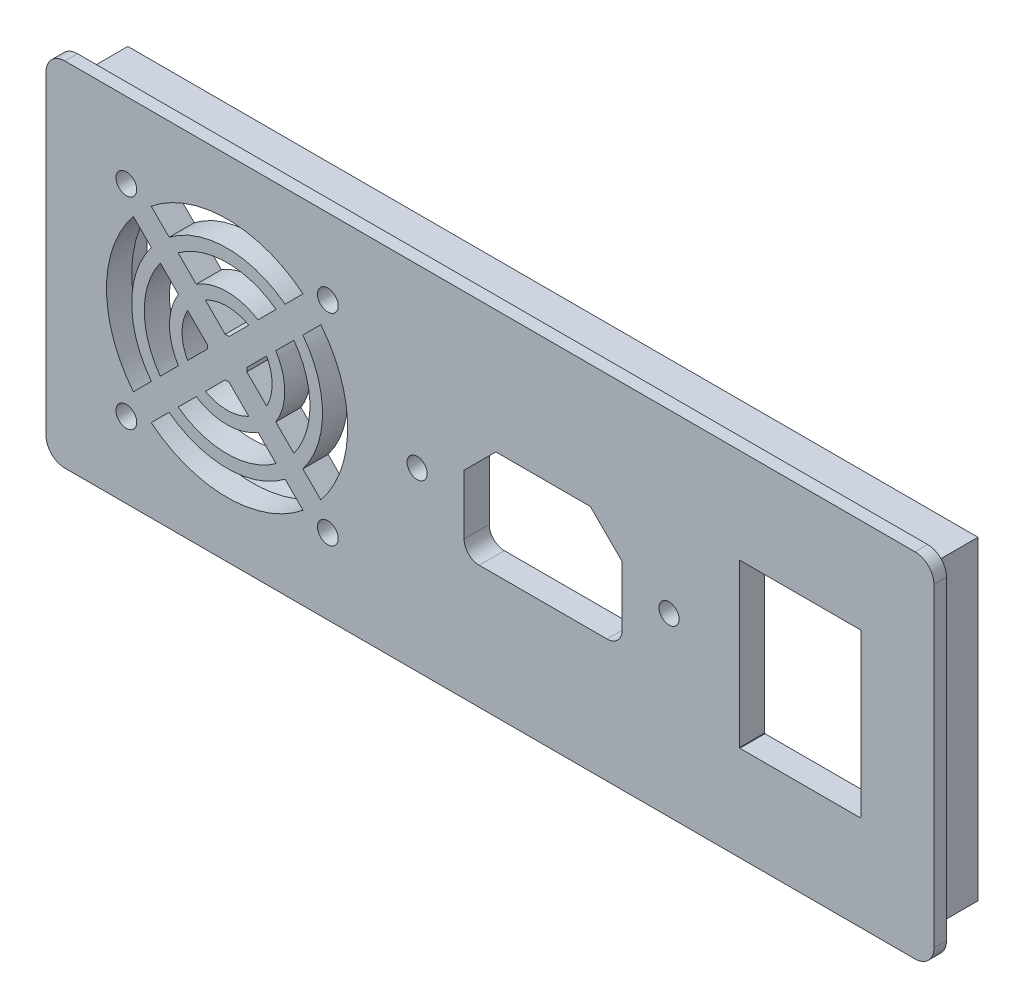
SolidWorks part; units mm, degrees
ref_plane "Alzado" through (0, 0, 0) normal (0, 0, 1) x (1, 0, 0)
ref_plane "Planta" through (0, 0, 0) normal (0, 1, 0) x (1, 0, 0)
ref_plane "Vista lateral" through (0, 0, 0) normal (1, 0, 0) x (0, 0, -1)
sketch "Croquis1" plane through (0, 0, 0) normal (0, 0, 1) x (1, 0, 0)
  line L0 (67.7484, -25.0621) -> (-67.2516, -25.0621)
  line L1 (67.7484, -25.0621) -> (67.7484, 24.9379)
  line L2 (67.7484, 24.9379) -> (-67.2516, 24.9379)
  line L3 (-67.2516, -25.0621) -> (-67.2516, 24.9379)
  line L4 (40.3202, -12.5326) -> (40.3202, -12.5916) construction
  line L5 (40.2702, -12.5326) -> (40.3202, -12.5326) construction
  line L6 (40.2702, 12.4674) -> (40.2702, -12.5326) construction
  line L7 (58.7702, 12.4674) -> (40.2702, 12.4674) construction
  line L8 (58.7702, -12.5326) -> (58.7702, 12.4674) construction
  line L9 (58.7202, -12.5326) -> (58.7702, -12.5326) construction
  line L10 (58.7202, -12.5916) -> (58.7202, -12.5326) construction
  line L11 (40.3202, -12.5916) -> (58.7202, -12.5916) construction
  line L12 (16.0269, 7.9879) -> (1.3453, 7.9879) construction
  line L13 (20.8361, 3.1787) -> (16.0269, 7.9879) construction
  line L14 (20.8361, -6.1121) -> (20.8361, 3.1787) construction
  line L15 (-1.4639, -8.1121) -> (18.8361, -8.1121) construction
  line L16 (-3.4639, 3.1787) -> (-3.4639, -6.1121) construction
  line L17 (1.3453, 7.9879) -> (-3.4639, 3.1787) construction
  line L59 (59.1702, 12.8674) -> (39.8702, 12.8674)
  line L60 (16.1926, 8.3879) -> (1.1796, 8.3879)
  line L61 (1.1796, 8.3879) -> (-3.8639, 3.3444)
  line L62 (-3.8639, 3.3444) -> (-3.8639, -6.1121)
  line L63 (-1.4639, -8.5121) -> (18.8361, -8.5121)
  line L64 (21.2361, -6.1121) -> (21.2361, 3.3444)
  line L65 (21.2361, 3.3444) -> (16.1926, 8.3879)
  line L66 (39.8702, 12.8674) -> (39.8702, -12.9326)
  line L67 (39.8702, -12.9326) -> (39.9202, -12.9326)
  line L68 (39.9202, -12.9326) -> (39.9202, -12.9916)
  line L69 (39.9202, -12.9916) -> (59.1202, -12.9916)
  line L70 (59.1202, -12.9916) -> (59.1202, -12.9326)
  line L71 (59.1202, -12.9326) -> (59.1702, -12.9326)
  line L72 (59.1702, -12.9326) -> (59.1702, 12.8674)
  line L73 (-67.2516, -0.0621) -> (67.7484, -0.0621) construction
  line L74 (8.6861, 8.3879) -> (8.6861, -8.5121) construction
  line L75 (49.5202, 12.8674) -> (49.5202, -12.9916) construction
  line L76 (-38.3584, -0.3687) -> (-35.2252, -3.5019)
  line L77 (-44.6285, -0.3687) -> (-47.7616, -3.5019)
  line L78 (-29.4406, 14.8191) -> (-32.2887, 11.971)
  line L79 (-26.6122, 11.9907) -> (-29.4603, 9.1426)
  line L80 (-56.3747, 11.9907) -> (-53.5265, 9.1426)
  line L81 (-53.5462, 14.8191) -> (-50.6981, 11.971)
  line L82 (-41.8, -3.1972) -> (-44.9332, -6.3303)
  line L83 (-41.1868, -3.1972) -> (-38.0536, -6.3303)
  line L84 (-30.8889, 7.714) -> (-33.7656, 4.8373)
  line L85 (-33.7174, 10.5424) -> (-36.5941, 7.6657)
  line L86 (-49.2695, 10.5424) -> (-46.3928, 7.6657)
  line L87 (-52.0979, 7.714) -> (-49.2212, 4.8373)
  line L88 (-53.5265, -9.2668) -> (-56.3747, -12.1149)
  line L89 (-50.6981, -12.0952) -> (-53.5462, -14.9434)
  line L90 (-32.2887, -12.0952) -> (-29.4406, -14.9434)
  line L91 (-29.4603, -9.2668) -> (-26.6122, -12.1149)
  line L92 (-33.7656, -4.9615) -> (-30.8889, -7.8382)
  line L93 (-36.5941, -7.7899) -> (-33.7174, -10.6666)
  line L94 (-46.3928, -7.7899) -> (-49.2695, -10.6666)
  line L95 (-49.2212, -4.9615) -> (-52.0979, -7.8382)
  line L96 (-47.7616, 3.3777) -> (-44.6285, 0.2445)
  line L97 (-44.9332, 6.2061) -> (-41.8, 3.0729)
  line L98 (-38.0536, 6.2061) -> (-41.1868, 3.0729)
  line L99 (-35.2252, 3.3777) -> (-38.3584, 0.2445)
  circle A0 centre (-57.4934, 15.9379) radius 1.65
  circle A1 centre (-25.4934, 15.9379) radius 1.65
  arc A2 (-56.3747, 11.9907) -> (-56.3747, -12.1149) centre (-41.4934, -0.0621) ccw
  circle A3 centre (-25.4934, -16.0621) radius 1.65
  circle A4 centre (-57.4934, -16.0621) radius 1.65
  arc A5 (18.8361, -8.1121) -> (20.8361, -6.1121) centre (18.8361, -6.1121) ccw construction
  arc A6 (-3.4639, -6.1121) -> (-1.4639, -8.1121) centre (-1.4639, -6.1121) ccw construction
  circle A40 centre (28.6861, -0.0621) radius 1.6
  circle A41 centre (-11.3139, -0.0621) radius 1.6
  arc A42 (-3.8639, -6.1121) -> (-1.4639, -8.5121) centre (-1.4639, -6.1121) ccw
  arc A43 (18.8361, -8.5121) -> (21.2361, -6.1121) centre (18.8361, -6.1121) ccw
  arc A44 (-32.2887, 11.971) -> (-50.6981, 11.971) centre (-41.4934, -0.0621) ccw
  arc A46 (-38.0536, 6.2061) -> (-44.9332, 6.2061) centre (-41.4934, -0.0621) ccw
  arc A47 (-41.1868, 3.0729) -> (-41.8, 3.0729) centre (-41.4934, -0.0621) ccw
  arc A49 (-33.7174, 10.5424) -> (-49.2695, 10.5424) centre (-41.4934, -0.0621) ccw
  arc A50 (-36.5941, 7.6657) -> (-46.3928, 7.6657) centre (-41.4934, -0.0621) ccw
  arc A52 (-44.6285, 0.2445) -> (-44.6285, -0.3687) centre (-41.4934, -0.0621) ccw
  circle A53 centre (-41.4934, -0.0621) radius 3.15 construction
  arc A54 (-41.8, -3.1972) -> (-41.1868, -3.1972) centre (-41.4934, -0.0621) ccw
  arc A55 (-38.3584, -0.3687) -> (-38.3584, 0.2445) centre (-41.4934, -0.0621) ccw
  arc A56 (-47.7616, 3.3777) -> (-47.7616, -3.5019) centre (-41.4934, -0.0621) ccw
  circle A57 centre (-41.4934, -0.0621) radius 7.15 construction
  circle A58 centre (-41.4934, -0.0621) radius 13.15 construction
  circle A59 centre (-41.4934, -0.0621) radius 15.15 construction
  arc A60 (-49.2212, 4.8373) -> (-49.2212, -4.9615) centre (-41.4934, -0.0621) ccw
  arc A61 (-53.5265, 9.1426) -> (-53.5265, -9.2668) centre (-41.4934, -0.0621) ccw
  arc A62 (-52.0979, 7.714) -> (-52.0979, -7.8382) centre (-41.4934, -0.0621) ccw
  arc A63 (-44.9332, -6.3303) -> (-38.0536, -6.3303) centre (-41.4934, -0.0621) ccw
  arc A64 (-46.3928, -7.7899) -> (-36.5941, -7.7899) centre (-41.4934, -0.0621) ccw
  arc A65 (-49.2695, -10.6666) -> (-33.7174, -10.6666) centre (-41.4934, -0.0621) ccw
  arc A66 (-50.6981, -12.0952) -> (-32.2887, -12.0952) centre (-41.4934, -0.0621) ccw
  arc A67 (-30.8889, -7.8382) -> (-30.8889, 7.714) centre (-41.4934, -0.0621) ccw
  arc A68 (-29.4603, -9.2668) -> (-29.4603, 9.1426) centre (-41.4934, -0.0621) ccw
  arc A69 (-33.7656, -4.9615) -> (-33.7656, 4.8373) centre (-41.4934, -0.0621) ccw
  arc A70 (-35.2252, -3.5019) -> (-35.2252, 3.3777) centre (-41.4934, -0.0621) ccw
  arc A71 (-29.4406, 14.8191) -> (-53.5462, 14.8191) centre (-41.4934, -0.0621) ccw
  circle A72 centre (-41.4934, -0.0621) radius 19.15 construction
  arc A73 (-26.6122, -12.1149) -> (-26.6122, 11.9907) centre (-41.4934, -0.0621) ccw
  arc A74 (-53.5462, -14.9434) -> (-29.4406, -14.9434) centre (-41.4934, -0.0621) ccw
  point P16 (-34.3434, -0.0621)
  point P35 (-26.3434, -0.0621)
  point P39 (-28.3434, -0.0621)
  point P78 (-38.3434, -0.0621)
  point P119 (-23.1802, 5.5368)
  dimension "D1" = 135
  dimension "D2" = 50
extrude "Saliente-Extruir1" add sketch "Croquis1" along normal blind 4
sketch "Croquis2" plane through (0, 0, 4) normal (0, 0, 1) x (1, 0, 0)
  line L24 (-67.2516, 24.9379) -> (67.7484, 24.9379)
  line L25 (-67.2516, 24.9379) -> (-67.2516, -25.0621)
  line L26 (-67.2516, -25.0621) -> (67.7484, -25.0621)
  line L27 (70.7484, -28.0621) -> (70.7484, 27.9379)
  line L28 (-70.2516, -28.0621) -> (70.7484, -28.0621)
  line L29 (-70.2516, 27.9379) -> (-70.2516, -28.0621)
  line L30 (70.7484, 27.9379) -> (-70.2516, 27.9379)
  line L31 (70.7484, -25.0621) -> (70.7484, 24.9379)
  line L32 (-67.2516, -28.0621) -> (67.7484, -28.0621)
  line L33 (-70.2516, 24.9379) -> (-70.2516, -25.0621)
  line L34 (67.7484, 27.9379) -> (-67.2516, 27.9379)
  line L35 (67.7484, 24.9379) -> (67.7484, -25.0621)
  arc A0 (70.7484, 24.9379) -> (67.7484, 27.9379) centre (67.7484, 24.9379) ccw
  arc A1 (70.7484, -25.0621) -> (67.7484, -28.0621) centre (67.7484, -25.0621) cw
  arc A2 (-67.2516, -28.0621) -> (-70.2516, -25.0621) centre (-67.2516, -25.0621) cw
  arc A3 (-70.2516, 24.9379) -> (-67.2516, 27.9379) centre (-67.2516, 24.9379) cw
  dimension "D2" = 3
  dimension "D1" = 3
extrude "Saliente-Extruir2" add sketch "Croquis2" against normal blind 2
sketch "Croquis3" plane through (0, 0, 0) normal (0, 0, -1) x (-1, 0, 0)
  line L0 (-64.7484, 16.9379) -> (-64.7484, -17.0621)
  line L1 (-67.7484, 24.9379) -> (67.2516, 24.9379)
  line L2 (-67.7484, 24.9379) -> (-67.7484, -25.0621)
  line L3 (-67.7484, -25.0621) -> (67.2516, -25.0621)
  line L4 (67.2516, 24.9379) -> (67.2516, -25.0621)
  line L5 (-59.7484, -22.0621) -> (59.2516, -22.0621)
  line L6 (64.2516, 16.9379) -> (64.2516, -17.0621)
  line L7 (-59.7484, 21.9379) -> (59.2516, 21.9379)
  line L8 (-64.7484, 21.9379) -> (-64.7484, -22.0621) construction
  line L9 (-64.7484, 21.9379) -> (64.2516, 21.9379) construction
  line L10 (-59.7484, 21.9379) -> (-64.7484, 16.9379)
  line L11 (-64.7484, -22.0621) -> (64.2516, -22.0621) construction
  line L12 (-64.7484, -17.0621) -> (-59.7484, -22.0621)
  line L13 (64.2516, 21.9379) -> (64.2516, -22.0621) construction
  line L14 (59.2516, 21.9379) -> (64.2516, 16.9379)
  line L15 (59.2516, -22.0621) -> (64.2516, -17.0621)
  line L16 (-67.7484, 24.9379) -> (-62.2484, 19.4379) construction
  line L17 (67.2516, 24.9379) -> (61.7516, 19.4379) construction
  line L18 (61.7516, -19.5621) -> (67.2516, -25.0621) construction
  line L19 (-62.2484, -19.5621) -> (-67.7484, -25.0621) construction
  circle A0 centre (-64.9984, 22.1879) radius 0.85
  circle A1 centre (64.5016, 22.1879) radius 0.85
  circle A2 centre (-64.9984, -22.3121) radius 0.85
  circle A3 centre (64.5016, -22.3121) radius 0.85
  dimension "D1" = 1.7
extrude "Saliente-Extruir3" add sketch "Croquis3" along normal blind 6
